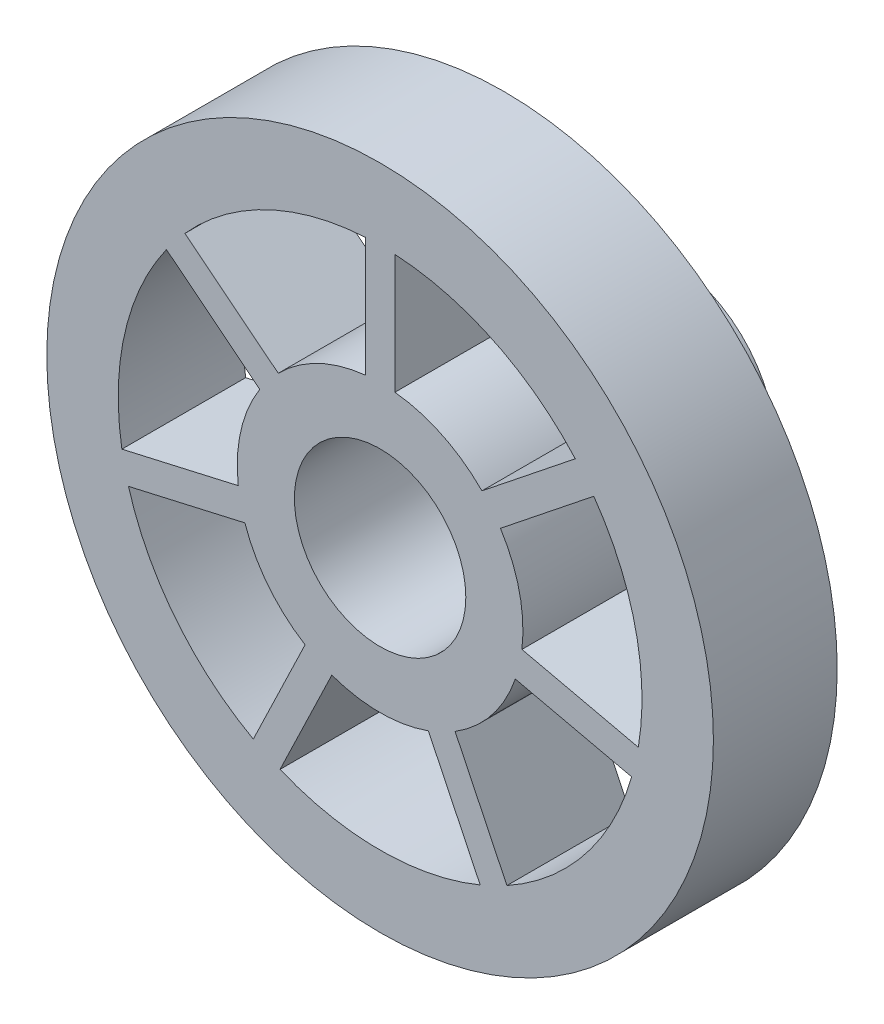
SolidWorks part; units mm, degrees
ref_plane "Front Plane" through (0, 0, 0) normal (0, 0, 1) x (1, 0, 0)
ref_plane "Top Plane" through (0, 0, 0) normal (0, 1, 0) x (1, 0, 0)
ref_plane "Right Plane" through (0, 0, 0) normal (1, 0, 0) x (0, 0, -1)
sketch "Sketch1" plane through (0, 0, 0) normal (0, 0, 1) x (1, 0, 0)
  line L0 (0, 11.3248) -> (0, 9.3248) construction
  line L5 (8.8684, 2.8815) -> (8.2581, 2.6832) construction
  line L10 (5.481, -7.5439) -> (5.1038, -7.0248) construction
  line L15 (-5.481, -7.5439) -> (-5.1038, -7.0248) construction
  line L20 (-10.7705, 3.4995) -> (-8.2581, 2.6832) construction
  circle A0 centre (0, 0) radius 11.5
  circle A1 centre (0, 6.5) radius 1.75
  circle A2 centre (6.5, 0) radius 1.75
  circle A3 centre (0, -6.5) radius 1.75
  circle A4 centre (-6.5, 0) radius 1.75
  point P14 (0, 0)
  point P44 (0, 0)
  dimension "D1" = 23
  dimension "D2" = 3.5
  dimension "D4" = 6.5
  dimension "D3" = 4
  dimension "D7" = 5
extrude "Boss-Extrude2" add sketch "Sketch1" along normal blind 6
sketch "Sketch2" plane through (0, 0, 6) normal (0, 0, 1) x (1, 0, 0)
  line L0 (10.8075, -3.9303) -> (9.0755, -2.9303)
  line L1 (-2, 11.3248) -> (2, 11.3248)
  line L2 (-2, 11.3248) -> (-2, 9.3248)
  line L3 (-2, 9.3248) -> (2, 9.3248)
  line L4 (2, 11.3248) -> (2, 9.3248)
  line L5 (10.8075, -3.9303) -> (8.8075, -7.3944)
  line L6 (9.0755, -2.9303) -> (7.0755, -6.3944)
  line L7 (8.8075, -7.3944) -> (7.0755, -6.3944)
  line L8 (-8.8075, -7.3944) -> (-7.0755, -6.3944)
  line L9 (-8.8075, -7.3944) -> (-10.8075, -3.9303)
  line L10 (-7.0755, -6.3944) -> (-9.0755, -2.9303)
  line L11 (-10.8075, -3.9303) -> (-9.0755, -2.9303)
  circle A0 centre (0, 0) radius 11.5 construction
  circle A1 centre (0, 0) radius 11.5
  point P16 (0, 0)
  point P24 (0, 0)
  dimension "D1" = 4
  dimension "D2" = 2
  dimension "D3" = 3
extrude "Boss-Extrude3" add sketch "Sketch2" along normal blind 12 contours L4 L1 L2 L3 | L1 M11 | L5 M11 | L7 L5 L0 L6 | L9 M11 | L11 L9 L8 L10
sketch "Sketch3" plane through (0, 0, 18) normal (0, 0, 1) x (1, 0, 0)
  line L0 (-1.5577, 14.9189) -> (-1.5577, 27.4559)
  line L1 (1.5577, 14.9189) -> (1.5577, 27.4559)
  line L2 (10.6929, 10.5196) -> (20.4947, 18.3363)
  line L3 (12.6353, 8.084) -> (22.437, 15.9006)
  line L4 (14.8915, -1.8012) -> (27.1141, -4.5909)
  line L5 (14.1982, -4.8384) -> (26.4209, -7.6281)
  line L6 (7.8765, -12.7656) -> (13.316, -24.061)
  line L7 (5.0697, -14.1173) -> (10.5092, -25.4127)
  line L8 (-5.0697, -14.1173) -> (-10.5092, -25.4127)
  line L9 (-7.8765, -12.7656) -> (-13.316, -24.061)
  line L10 (-14.1982, -4.8384) -> (-26.4209, -7.6281)
  line L11 (-14.8915, -1.8012) -> (-27.1141, -4.5909)
  line L12 (-12.6353, 8.084) -> (-22.437, 15.9006)
  line L13 (-10.6929, 10.5196) -> (-20.4947, 18.3363)
  circle A0 centre (0, 0) radius 9
  circle A1 centre (0, 0) radius 35
  circle A2 centre (0, 0) radius 27.5
  circle A3 centre (0, 0) radius 15
  point P38 (0, 0)
  point P39 (0.9044, 1.134)
  dimension "D1" = 7
  dimension "D2" = 18
  dimension "D3" = 30
  dimension "D4" = 55
extrude "Boss-Extrude5" add sketch "Sketch3" along normal blind 12 and the other way blind 1
